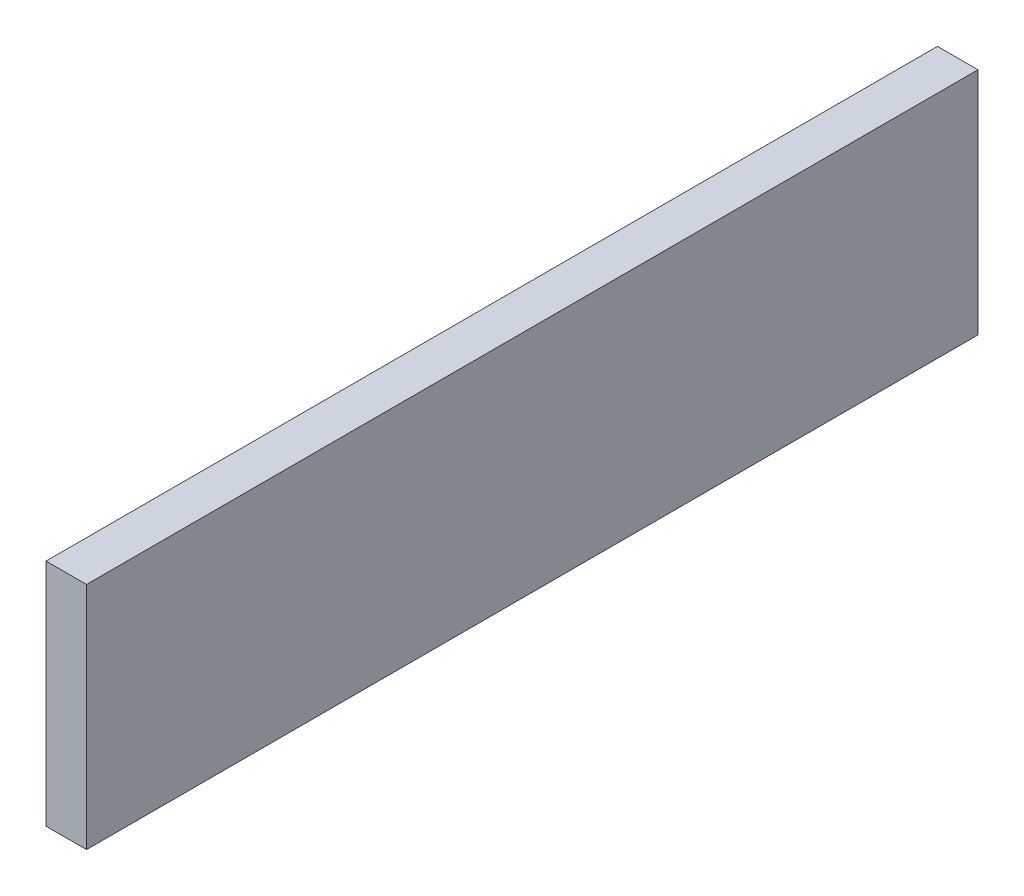
SolidWorks part; units mm, degrees
ref_plane "Front Plane" through (0, 0, 0) normal (0, 0, 1) x (1, 0, 0)
ref_plane "Top Plane" through (0, 0, 0) normal (0, 1, 0) x (1, 0, 0)
ref_plane "Right Plane" through (0, 0, 0) normal (1, 0, 0) x (0, 0, -1)
sketch "Sketch1" plane through (0, 0, 0) normal (1, 0, 0) x (0, 0, -1)
  line L1 (0, 107.95) -> (419.1, 107.95)
  line L2 (0, 107.95) -> (0, 0)
  line L3 (0, 0) -> (419.1, 0)
  line L4 (419.1, 107.95) -> (419.1, 0)
  dimension "D1" = 107.95
  dimension "D2" = 419.1
extrude "Boss-Extrude1" add sketch "Sketch1" along normal blind 19.05
